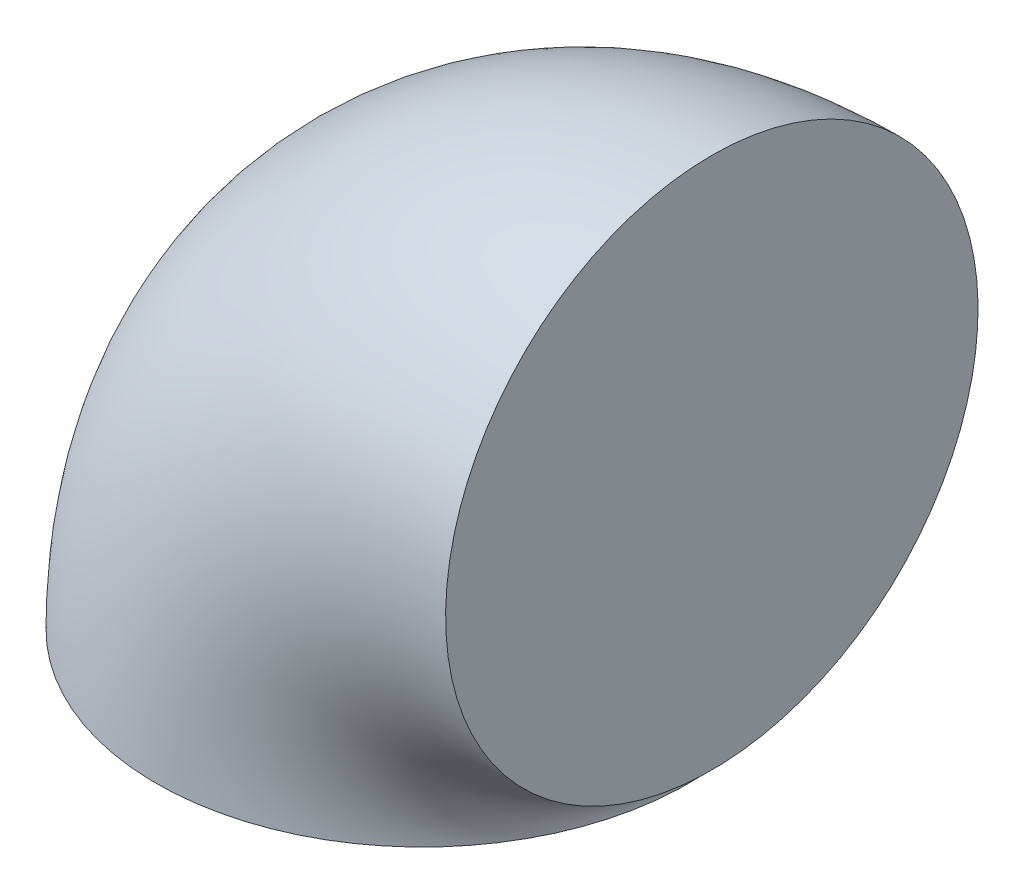
SolidWorks part; units mm, degrees
ref_plane "Plano frontal" through (0, 0, 0) normal (0, 0, 1) x (1, 0, 0)
ref_plane "Plano superior" through (0, 0, 0) normal (0, 1, 0) x (1, 0, 0)
ref_plane "Plano direito" through (0, 0, 0) normal (1, 0, 0) x (0, 0, -1)
sketch "Esboço1" plane through (0, 0, 0) normal (0, 1, 0) x (1, 0, 0)
  line L0 (0, 0) -> (53.8, 0)
  line L1 (53.8, 0) -> (53.8, 20)
  circle A0 centre (0, 0) radius 49.5
revolve "Revolução1" add sketch "Esboço1" angle 90 about L1
